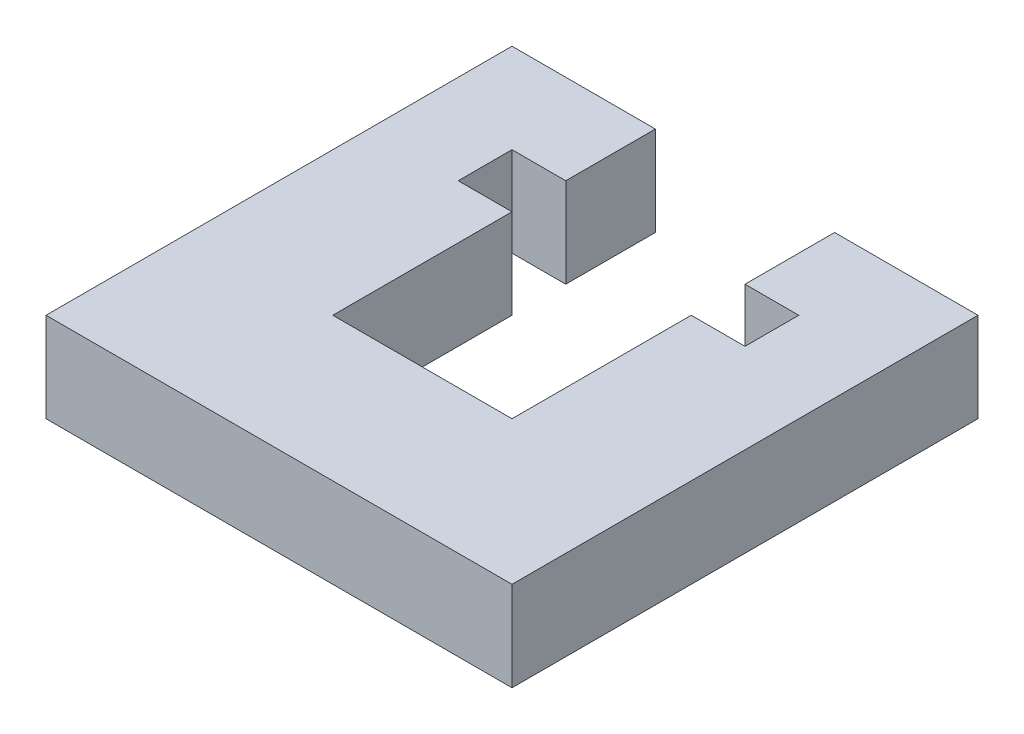
SolidWorks part; units mm, degrees
ref_plane "前视基准面" through (0, 0, 0) normal (0, 0, 1) x (1, 0, 0)
ref_plane "上视基准面" through (0, 0, 0) normal (0, 1, 0) x (1, 0, 0)
ref_plane "右视基准面" through (0, 0, 0) normal (1, 0, 0) x (0, 0, -1)
sketch "草图1" plane through (0, 0, 0) normal (0, 1, 0) x (1, 0, 0)
  line L0 (0, 26) -> (0, 0)
  line L1 (0, 0) -> (26, 0)
  line L2 (26, 0) -> (26, 26)
  line L3 (26, 26) -> (18, 26)
  line L4 (18, 26) -> (18, 21)
  line L5 (18, 8) -> (8, 8)
  line L6 (8, 8) -> (8, 18)
  line L7 (8, 26) -> (0, 26)
  line L8 (8, 21) -> (8, 26)
  line L9 (21, 21) -> (18, 21)
  line L10 (21, 21) -> (21, 18)
  line L11 (21, 18) -> (18, 18)
  line L12 (5, 21) -> (5, 18)
  line L13 (21, 21) -> (5, 18) construction
  line L14 (21, 18) -> (5, 21) construction
  line L15 (18, 18) -> (18, 8)
  line L16 (8, 21) -> (5, 21)
  line L17 (8, 18) -> (5, 18)
  point P8 (5, 19.5)
  point P14 (13, 19.5)
  dimension "D1" = 8
  dimension "D2" = 8
  dimension "D3" = 8
  dimension "D4" = 26
  dimension "D5" = 26
  dimension "D6" = 10
  dimension "D7" = 3
  dimension "D8" = 3
  dimension "D9" = 3
  dimension "D10" = 10
extrude "凸台-拉伸1" add sketch "草图1" along normal blind 5
